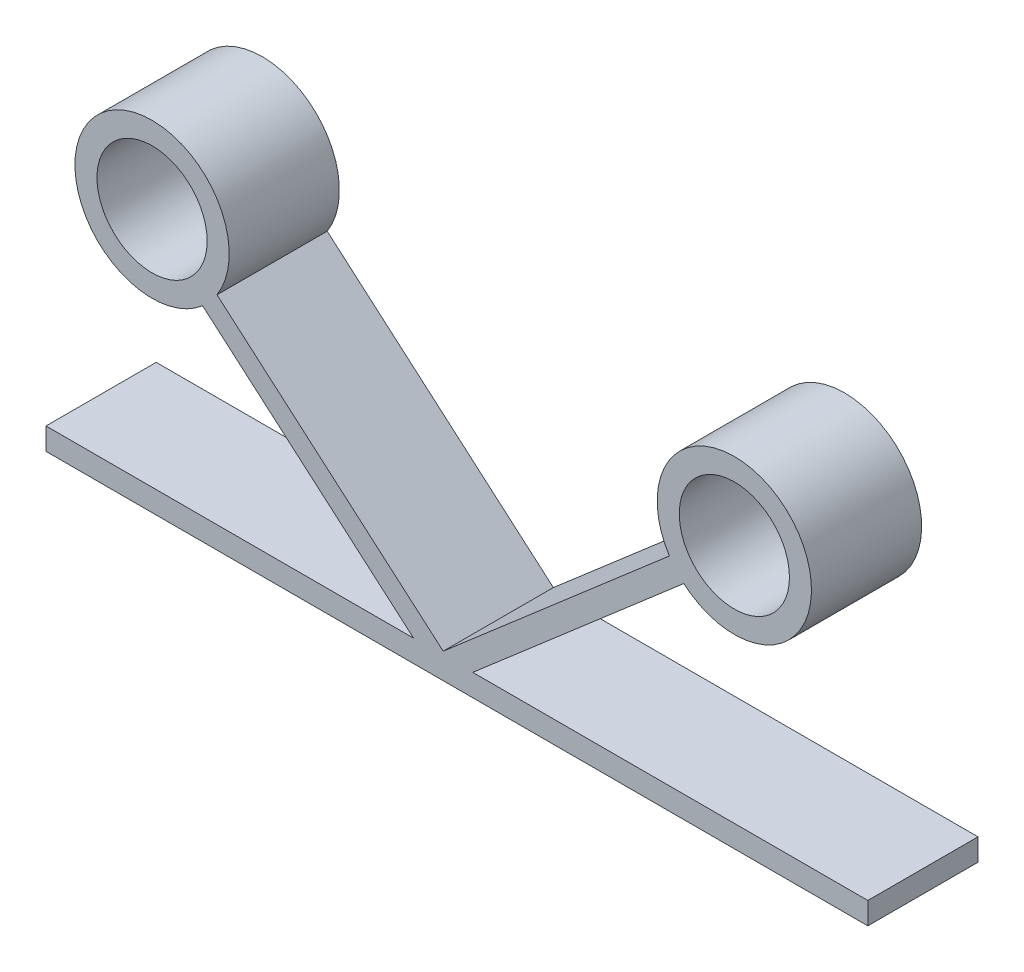
SolidWorks part; units mm, degrees
material "Plain Carbon Steel"
ref_plane "Front Plane" through (0, 0, 0) normal (0, 0, 1) x (1, 0, 0)
ref_plane "Top Plane" through (0, 0, 0) normal (0, 1, 0) x (1, 0, 0)
ref_plane "Right Plane" through (0, 0, 0) normal (1, 0, 0) x (0, 0, -1)
sketch "Sketch1" plane through (0, 0, 0) normal (0, 0, 1) x (1, 0, 0)
  line L0 (-66.06, 0) -> (66.06, 0) construction
  circle A0 centre (-66.06, 0) radius 12.5
  circle A1 centre (66.06, 0) radius 12.5
  point P4 (0, 0)
  dimension "D1" = 132.12
  dimension "D2" = 25
  dimension "D3" = 25
extrude "Extrude-Thin1" add sketch "Sketch1" along normal mid plane 25 thin
sketch "Sketch2" plane through (0, 0, 0) normal (0, 0, 1) x (1, 0, 0)
  line L0 (-55.4686, -9.1555) -> (0, -57.104)
  line L1 (0, -57.104) -> (55.3251, -9.2795)
  line L2 (-90.1215, -57.104) -> (96.3461, -57.104)
extrude "Extrude-Thin2" add sketch "Sketch2" along normal mid plane 25 thin thin type mid plane wall 5
sketch "Sketch3" plane through (0, 0, 0) normal (0, 0, 1) x (1, 0, 0)
  line L0 (-90.1215, -59.604) -> (-0.9308, -59.604) construction
  line L1 (-4.4348, -59.604) -> (4.6101, -59.604)
  line L2 (-4.4348, -59.604) -> (-4.4348, -64.3858)
  line L3 (-4.4348, -64.3858) -> (4.6101, -64.3858)
  line L4 (4.6101, -59.604) -> (4.6101, -64.3858)
extrude "Cut-Extrude1" cut sketch "Sketch3" against normal through all both and the other way through all
